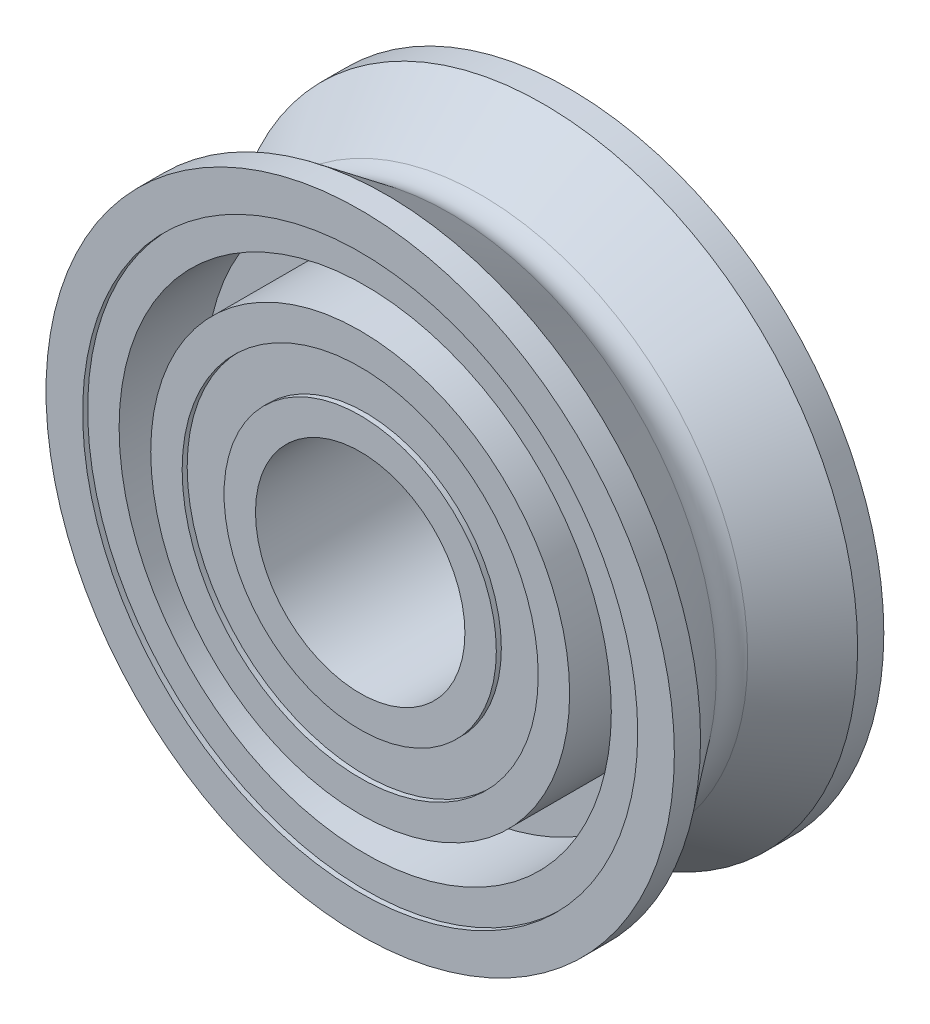
SolidWorks part; units mm, degrees
ref_plane "Front" through (0, 0, 0) normal (0, 0, 1) x (1, 0, 0)
ref_plane "Top" through (0, 0, 0) normal (0, 1, 0) x (1, 0, 0)
ref_plane "Right" through (0, 0, 0) normal (1, 0, 0) x (0, 0, -1)
sketch "Sketch1" plane through (0, 0, 0) normal (1, 0, 0) x (0, 0, -1)
  line L0 (1.1906, 4.7625) -> (1.5875, 4.7625)
  line L1 (-1.1906, 4.7625) -> (-1.5875, 4.7625)
  line L2 (-1.1906, 4.7625) -> (-0.2381, 4.0481)
  line L3 (1.5113, 2.6988) -> (1.5113, 2.0637)
  line L4 (1.5875, 1.5875) -> (-1.5875, 1.5875)
  line L5 (-1.5113, 2.0638) -> (-1.5113, 2.6988)
  line L6 (1.1906, 4.7625) -> (0.2381, 4.0481)
  line L7 (-1.5875, 4.2069) -> (-1.5113, 4.2069)
  line L8 (-1.5875, 0) -> (1.5875, 0) construction
  line L9 (-1.5113, 4.2069) -> (-1.5113, 3.7306)
  line L10 (1.5875, 4.7625) -> (1.5875, 4.2069)
  line L11 (1.5875, 4.2069) -> (1.5113, 4.2069)
  line L12 (-1.5113, 2.0638) -> (-1.5875, 2.0638)
  line L13 (-1.5875, 2.0638) -> (-1.5875, 1.5875)
  line L14 (0, 3.9688) -> (0, -3.9688) construction
  line L15 (1.5875, 2.0637) -> (1.5113, 2.0637)
  line L16 (1.5875, 2.0637) -> (1.5875, 1.5875)
  line L17 (-1.5875, 4.7625) -> (-1.5875, -4.7625) construction
  line L18 (-1.5113, 3.7306) -> (-0.1984, 3.7306)
  line L19 (-0.1984, 3.7306) -> (-0.1984, 3.175)
  line L20 (-0.1984, 3.175) -> (-1.5875, 3.175)
  line L21 (-1.5875, 4.2069) -> (-1.5875, 4.7625)
  line L22 (1.5113, 3.7306) -> (0.1984, 3.7306)
  line L23 (0.1984, 3.7306) -> (0.1984, 3.175)
  line L24 (0.1984, 3.175) -> (1.5875, 3.175)
  line L25 (1.5113, 4.2069) -> (1.5113, 3.7306)
  line L26 (-1.5113, 2.6988) -> (-1.5875, 2.6988)
  line L27 (-1.5875, 2.6988) -> (-1.5875, 3.175)
  line L28 (1.5875, 3.175) -> (1.5875, 2.6988)
  line L29 (1.5875, 2.6988) -> (1.5113, 2.6988)
  arc A0 (-0.2381, 4.0481) -> (0.2381, 4.0481) centre (0, 4.3656) ccw
  circle A1 centre (0, 4.3656) radius 0.3969 construction
  circle A2 centre (0, 0) radius 1.5875 construction
  circle A3 centre (0, 0) radius 2.0638 construction
  circle A4 centre (0, 0) radius 3.175 construction
  circle A5 centre (0, -4.3656) radius 0.3969 construction
  point P28 (-1.5875, 0)
  dimension "Rope Dia" = 0.7937
  dimension "Shaft Dia" = 3.175
  dimension "D1" = 4.1275
  dimension "D3" = 6.35
  dimension "Wd" = 3.175
  dimension "D8" = 0.3969
  dimension "Groove Dia" = 7.9375
  dimension "OD" = 9.525
  dimension "D6" = 0.0762
  dimension "D2" = 0.3969
revolve "Revolve1" add sketch "Sketch1" angle 360 about L8
sketch "Sketch2" plane through (0, 0, 0) normal (0, 0, 1) x (1, 0, 0)
  circle A0 centre (0, 0) radius 2.0638 construction
  circle A1 centre (0, 0) radius 2.0638
extrude "Cut-Extrude-Thin1" [suppressed] cut sketch "Sketch2" against normal through all and the other way through all thin contours A1
equation "\"D1@Sketch1\" = \"Shaft Dia@Sketch1\" * 1.3"
equation "\"D3@Sketch1\" = \"Shaft Dia@Sketch1\" * 2"
equation "\"D8@Sketch1\" = \"Wd@Sketch1\" * .125"
equation "\"D2@Sketch1\" = \"D8@Sketch1\""
